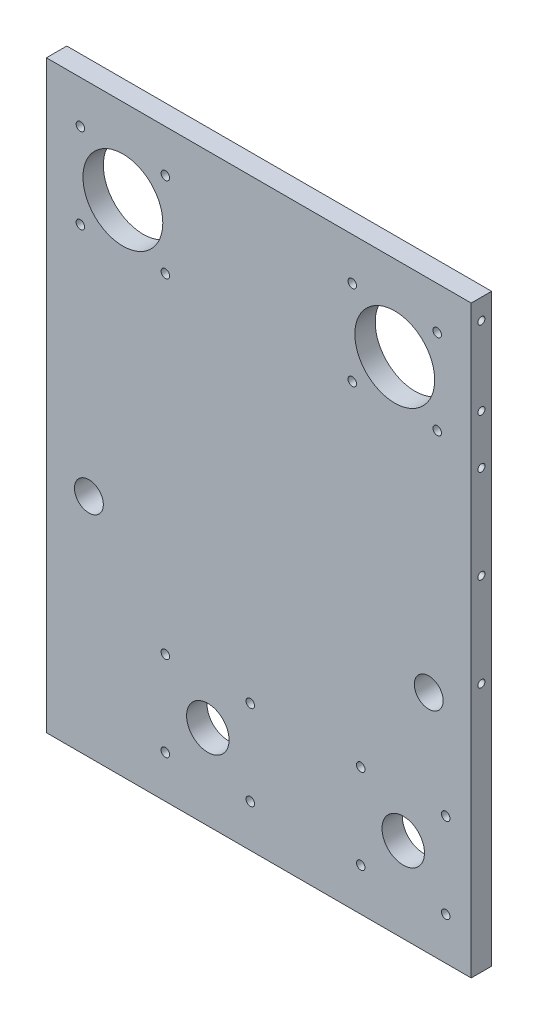
SolidWorks part; units mm, degrees
material "1.0545 (S355N)"
ref_plane "Front Plane" through (0, 0, 0) normal (0, 0, 1) x (1, 0, 0)
ref_plane "Top Plane" through (0, 0, 0) normal (0, 1, 0) x (1, 0, 0)
ref_plane "Right Plane" through (0, 0, 0) normal (1, 0, 0) x (0, 0, -1)
sketch "Sketch1" plane through (0, 0, 0) normal (0, 0, 1) x (1, 0, 0)
  line L0 (0, 715.3769) -> (0, -220.3769) construction
  line L1 (-125, 294) -> (125, 294)
  line L2 (125, 294) -> (125, -50)
  line L4 (125, -50) -> (-125, -50)
  line L6 (-125, -50) -> (-125, 294)
  circle A0 centre (-80, 244) radius 23.5
  circle A1 centre (80, 244) radius 23.5
  circle A2 centre (-100, 83) radius 8.5
  circle A4 centre (100, 83) radius 8.5
  circle A6 centre (-30, 0) radius 12.5
  circle A9 centre (85, 0) radius 12.5
  dimension "D9" = 47
  dimension "D5" = 17
  dimension "D10" = 344
  dimension "D11" = 25
  dimension "D2" = 211
  dimension "D7" = 25
  dimension "D14" = 40
  dimension "D1" = 250
  dimension "D3" = 160
  dimension "D4" = 200
  dimension "D6" = 50
  dimension "D8" = 294
  dimension "D13" = 50
extrude "Boss-Extrude1" add sketch "Sketch1" along normal blind 12
sketch "Sketch2" plane through (0, 0, 0) normal (0, 0, -1) x (-1, 0, 0)
  circle A0 centre (-80, 244) radius 23.5
  circle A1 centre (80, 244) radius 23.5
  circle A2 centre (-85, 0) radius 12.5
  circle A3 centre (30, 0) radius 12.5
  circle A4 centre (30, 0) radius 12.5 construction
  circle A5 centre (-85, 0) radius 12.5 construction
  circle A6 centre (-80, 244) radius 23.5 construction
  circle A7 centre (80, 244) radius 23.5 construction
  dimension "D5" = 47
  dimension "D1" = 244
  dimension "D2" = 50
  dimension "D3" = 160
  dimension "D4" = 165
sketch "Sketch6" plane through (-125, 0, 0) normal (-1, 0, 0) x (0, 0, 1)
  line L0 (12, 294) -> (0, 294) construction
  point P0 (6, 282)
  point P1 (6, 236)
  dimension "D1" = 6
  dimension "D2" = 12
  dimension "D3" = 58
hole_wizard "M5 Tapped Hole1" positions "Sketch3" profile "Sketch5" tap size "M5" standard "ISO"
sketch "Sketch3" plane through (-125, 0, 0) normal (-1, 0, 0) x (0, 0, 1)
  line L0 (12, 294) -> (12, -50) construction
  line L2 (12, 294) -> (0, 294) construction
  point P0 (6, 282)
  point P9 (6, 282)
  point P11 (6, 236)
  dimension "D1" = 6
  dimension "D2" = 12
sketch "Sketch5" plane through (-125, 282, 6) normal (0, 1, 0) x (0, 0, 1)
  line L0 (0, 0) -> (0, 16.2618)
  line L1 (0, 16.2618) -> (2.1, 15)
  line L2 (2.1, 15) -> (2.1, 0)
  line L5 (2.1, 0) -> (0, 0)
  line L10 (0, 16.2618) -> (-2.1, 15) construction
  line L11 (0, -6.35) -> (0, 107.95) construction
  dimension "Tap Drill Dia." = 4.2
  dimension "Tap Drill Depth" = 15
  dimension "Drill Angle" = 118
cosmetic thread "Hole Thread1" parameters "D1"=10, "D2"=5
cosmetic thread "Hole Thread33" parameters "D1"=10, "D2"=5
cosmetic thread "Hole Thread35" parameters "D1"=10, "D2"=5
mirror "Mirror1" about plane through (0, 0, 0) normal (1, 0, 0) of "M5 Tapped Hole1"
cosmetic thread "Hole Thread4" parameters "D1"=10, "D2"=5
cosmetic thread "Hole Thread34" parameters "D1"=10, "D2"=5
sketch "Sketch7" plane through (0, 0, 12) normal (0, 0, 1) x (1, 0, 0)
  line L0 (-80, 283.5963) -> (-80, 202.5134) construction
  line L1 (-127.2468, 244) -> (-34.1258, 244) construction
  line L2 (80, 283.5963) -> (80, 202.5134) construction
  line L3 (32.7532, 244) -> (125.8742, 244) construction
  line L4 (-30, 29.0045) -> (-30, -52.0784) construction
  line L5 (-74.4956, 0) -> (18.6254, 0) construction
  line L6 (85, 33.2354) -> (85, -47.8475) construction
  line L7 (93.0252, 0) -> (186.1462, 0) construction
  circle A1 centre (-80, 244) radius 23.5 construction
  circle A2 centre (80, 244) radius 23.5 construction
  circle A3 centre (-30, 0) radius 12.5 construction
  circle A4 centre (85, 0) radius 12.5 construction
  point P4 (-105, 269)
  point P5 (-55, 269)
  point P6 (-55, 219)
  point P7 (-105, 219)
  point P10 (-80, 244)
  point P15 (55, 269)
  point P16 (105, 269)
  point P17 (105, 219)
  point P18 (55, 219)
  point P19 (80, 244)
  point P27 (-55, 25)
  point P28 (-5, 25)
  point P29 (-5, -25)
  point P30 (-55, -25)
  point P31 (-30, 0)
  point P37 (60, 25)
  point P38 (110, 25)
  point P39 (110, -25)
  point P41 (60, -25)
  point P42 (85, 0)
  dimension "D1" = 50
  dimension "D2" = 50
  dimension "D3" = 50
  dimension "D4" = 50
  dimension "D5" = 50
  dimension "D6" = 50
  dimension "D7" = 50
  dimension "D8" = 50
hole_wizard "M6 Tapped Hole1" positions "Sketch8" profile "Sketch9" tap size "M6" standard "ISO" end condition through all
sketch "Sketch8" plane through (0, 0, 12) normal (0, 0, 1) x (1, 0, 0)
  point P0 (-105, 269)
  point P3 (-55, 269)
  point P6 (-55, 219)
  point P9 (-105, 219)
  point P12 (55, 219)
  point P15 (105, 219)
  point P18 (105, 269)
  point P21 (55, 269)
  point P24 (-55, 25)
  point P27 (-5, 25)
  point P30 (-5, -25)
  point P33 (-55, -25)
  point P36 (60, 25)
  point P39 (110, 25)
  point P42 (110, -25)
  point P45 (60, -25)
sketch "Sketch9" plane through (-105, 269, 12) normal (1, 0, 0) x (0, -1, 0)
  line L0 (0, 0) -> (0, 12)
  line L1 (0, 12) -> (2.5, 12)
  line L2 (2.5, 12) -> (2.5, 0)
  line L5 (2.5, 0) -> (0, 0)
  line L11 (0, -6.35) -> (0, 107.95) construction
  dimension "Thru Tap Drill Dia." = 5
  dimension "Thru Tap Drill Depth" = 12
cosmetic thread "Hole Thread7" parameters "D2"=6
cosmetic thread "Hole Thread8" parameters "D2"=6
cosmetic thread "Hole Thread9" parameters "D2"=6
cosmetic thread "Hole Thread10" parameters "D2"=6
cosmetic thread "Hole Thread11" parameters "D2"=6
cosmetic thread "Hole Thread12" parameters "D2"=6
cosmetic thread "Hole Thread13" parameters "D2"=6
cosmetic thread "Hole Thread14" parameters "D2"=6
cosmetic thread "Hole Thread15" parameters "D2"=6
cosmetic thread "Hole Thread16" parameters "D2"=6
cosmetic thread "Hole Thread17" parameters "D2"=6
cosmetic thread "Hole Thread18" parameters "D2"=6
cosmetic thread "Hole Thread19" parameters "D2"=6
cosmetic thread "Hole Thread20" parameters "D2"=6
cosmetic thread "Hole Thread21" parameters "D2"=6
cosmetic thread "Hole Thread22" parameters "D2"=6
sketch "Sketch10" plane through (0, -50, 0) normal (0, -1, 0) x (1, 0, 0)
  line L0 (144.5293, 6) -> (-144.5293, 6) construction
  line L1 (-125, 0) -> (125, 0) construction
  line L2 (125, 12) -> (125, 0) construction
  line L3 (-125, 12) -> (-125, 0) construction
  point P4 (113, 6)
  point P5 (67, 6)
  point P6 (-67, 6)
  point P7 (-113, 6)
  dimension "D1" = 6
  dimension "D2" = 12
  dimension "D3" = 58
  dimension "D4" = 12
  dimension "D5" = 58
hole_wizard "M5 Tapped Hole2" positions "Sketch14" profile "Sketch15" tap size "M5" standard "ISO"
sketch "Sketch14" plane through (0, -50, 0) normal (0, -1, 0) x (-1, 0, 0)
  point P0 (-113, -6)
  point P3 (-67, -6)
  point P6 (67, -6)
  point P9 (113, -6)
sketch "Sketch15" plane through (113, -50, 6) normal (1, 0, 0) x (0, 0, -1)
  line L0 (0, 0) -> (0, 16.2618)
  line L1 (0, 16.2618) -> (2.1, 15)
  line L2 (2.1, 15) -> (2.1, 0)
  line L5 (2.1, 0) -> (0, 0)
  line L10 (0, 16.2618) -> (-2.1, 15) construction
  line L11 (0, -6.35) -> (0, 107.95) construction
  dimension "Tap Drill Dia." = 4.2
  dimension "Tap Drill Depth" = 15
  dimension "Drill Angle" = 118
cosmetic thread "Hole Thread23" parameters "D1"=10, "D2"=5
cosmetic thread "Hole Thread24" parameters "D1"=10, "D2"=5
cosmetic thread "Hole Thread25" parameters "D1"=10, "D2"=5
cosmetic thread "Hole Thread26" parameters "D1"=10, "D2"=5
sketch "Sketch16" plane through (125, 0, 0) normal (1, 0, 0) x (0, 0, -1)
  line L0 (-6, 134.1353) -> (-6, 224.9071) construction
  line L1 (-12, -50) -> (-12, 294) construction
  line L2 (-12, 294) -> (0, 294) construction
  point P0 (-6, 207)
  point P1 (-6, 97)
  point P8 (-6, 152)
  dimension "D1" = 6
  dimension "D2" = 87
  dimension "D3" = 110
  dimension "D4" = 55
hole_wizard "M5 Tapped Hole3" positions "Sketch17" profile "Sketch19" tap size "M5" standard "ISO"
sketch "Sketch17" plane through (125, 0, 0) normal (1, 0, 0) x (0, 0, -1)
  point P0 (-6, 97)
  point P3 (-6, 152)
  point P6 (-6, 207)
sketch "Sketch19" plane through (125, 97, 6) normal (0, 1, 0) x (0, 0, -1)
  line L0 (0, 0) -> (0, 16.2618)
  line L1 (0, 16.2618) -> (2.1, 15)
  line L2 (2.1, 15) -> (2.1, 0)
  line L5 (2.1, 0) -> (0, 0)
  line L10 (0, 16.2618) -> (-2.1, 15) construction
  line L11 (0, -6.35) -> (0, 107.95) construction
  dimension "Tap Drill Dia." = 4.2
  dimension "Tap Drill Depth" = 15
  dimension "Drill Angle" = 118
cosmetic thread "Hole Thread27" parameters "D1"=10, "D2"=5
cosmetic thread "Hole Thread28" parameters "D1"=10, "D2"=5
cosmetic thread "Hole Thread29" parameters "D1"=10, "D2"=5
mirror "Mirror2" about plane through (0, 0, 0) normal (1, 0, 0) of "M5 Tapped Hole3"
cosmetic thread "Hole Thread30" parameters "D1"=10, "D2"=5
cosmetic thread "Hole Thread31" parameters "D1"=10, "D2"=5
cosmetic thread "Hole Thread32" parameters "D1"=10, "D2"=5
